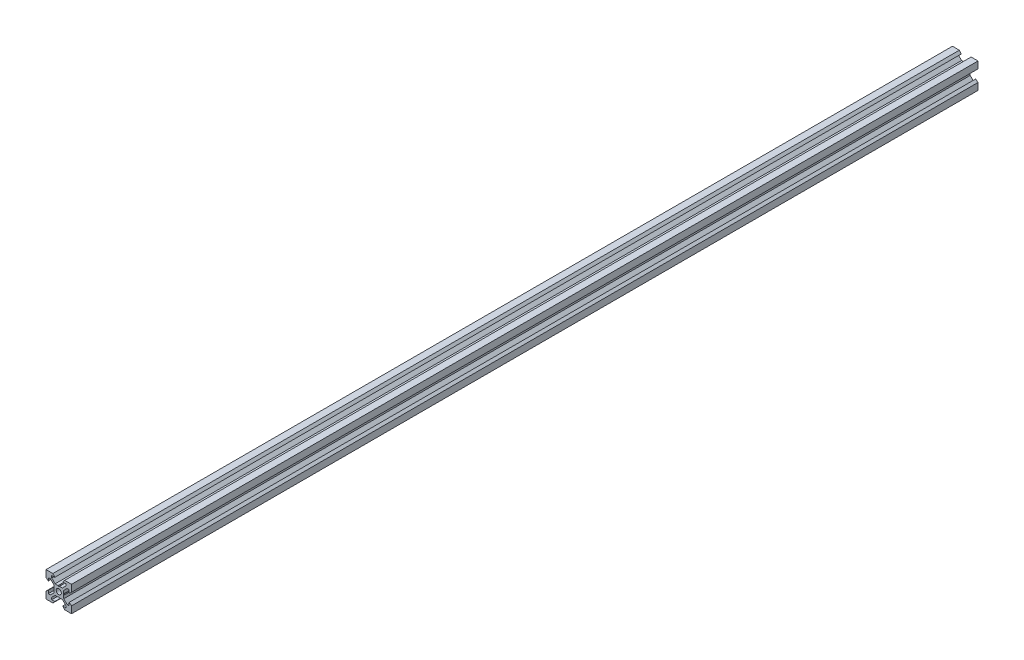
SolidWorks part; units mm, degrees
ref_plane "Front Plane" through (0, 0, 0) normal (0, 0, 1) x (1, 0, 0)
ref_plane "Top Plane" through (0, 0, 0) normal (0, 1, 0) x (1, 0, 0)
ref_plane "Right Plane" through (0, 0, 0) normal (1, 0, 0) x (0, 0, -1)
sketch "Sketch1" plane through (0, 0, 0) normal (0, 0, 1) x (1, 0, 0)
  line L0 (10, 10) -> (4.6104, 10) construction
  line L1 (10, 10) -> (10, 4.6104) construction
  line L2 (10, -10) -> (10, -4.6104) construction
  line L3 (10, -10) -> (4.6104, -10) construction
  line L4 (10, 10) -> (10, 4.6104)
  line L5 (6.5607, 5.5) -> (8.2, 5.5)
  line L6 (5.5, 8.2) -> (5.5, 6.5607)
  line L7 (10, 10) -> (4.6104, 10)
  line L8 (10, 10) -> (10, 4.6104)
  line L9 (6.5607, 5.5) -> (3.9, 2.8393)
  line L10 (5.5, 6.5607) -> (2.8393, 3.9)
  line L11 (10, 4.6104) -> (8.2, 3.1)
  line L12 (4.6104, 10) -> (3.1, 8.2)
  line L13 (8.2, 3.1) -> (8.2, 5.5)
  line L14 (3.1, 8.2) -> (5.5, 8.2)
  line L15 (-6.5607, 5.5) -> (-8.2, 5.5)
  line L16 (6.5607, -5.5) -> (8.2, -5.5)
  line L17 (3.1, -8.2) -> (5.5, -8.2)
  line L18 (8.2, -3.1) -> (8.2, -5.5)
  line L19 (4.6104, -10) -> (3.1, -8.2)
  line L20 (10, -4.6104) -> (8.2, -3.1)
  line L21 (0.5196, -3.9) -> (0, -3.6)
  line L22 (0.5196, 3.9) -> (0, 3.6)
  line L23 (3.6, 0) -> (3.9, -0.5196)
  line L24 (3.9, 0.5196) -> (3.6, 0)
  line L25 (3.9, 0.5196) -> (3.9, 2.8393)
  line L26 (2.8393, 3.9) -> (0.5196, 3.9)
  line L27 (3.9, -2.8393) -> (3.9, -0.5196)
  line L28 (2.8393, -3.9) -> (0.5196, -3.9)
  line L29 (5.5, -6.5607) -> (2.8393, -3.9)
  line L30 (6.5607, -5.5) -> (3.9, -2.8393)
  line L31 (10, -10) -> (10, -4.6104)
  line L32 (10, -10) -> (4.6104, -10)
  line L33 (5.5, -8.2) -> (5.5, -6.5607)
  line L34 (-6.5607, -5.5) -> (-8.2, -5.5)
  line L35 (10, -10) -> (10, -4.6104)
  line L36 (0, 0) -> (0, 8.2) construction
  line L37 (-10, -10) -> (-4.6104, -10) construction
  line L38 (-10, -10) -> (-10, -4.6104) construction
  line L39 (-10, 10) -> (-10, 4.6104) construction
  line L40 (-10, 10) -> (-4.6104, 10) construction
  line L41 (-10, -10) -> (-10, -4.6104)
  line L43 (-5.5, -8.2) -> (-5.5, -6.5607)
  line L44 (-10, -10) -> (-4.6104, -10)
  line L45 (-10, -10) -> (-10, -4.6104)
  line L46 (-6.5607, -5.5) -> (-3.9, -2.8393)
  line L47 (-5.5, -6.5607) -> (-2.8393, -3.9)
  line L48 (-2.8393, -3.9) -> (-0.5196, -3.9)
  line L49 (-3.9, -2.8393) -> (-3.9, -0.5196)
  line L50 (-2.8393, 3.9) -> (-0.5196, 3.9)
  line L51 (-3.9, 0.5196) -> (-3.9, 2.8393)
  line L52 (-3.9, 0.5196) -> (-3.6, 0)
  line L53 (-3.6, 0) -> (-3.9, -0.5196)
  line L54 (-0.5196, 3.9) -> (0, 3.6)
  line L55 (-0.5196, -3.9) -> (0, -3.6)
  line L56 (-10, -4.6104) -> (-8.2, -3.1)
  line L57 (-4.6104, -10) -> (-3.1, -8.2)
  line L58 (-8.2, -3.1) -> (-8.2, -5.5)
  line L59 (-3.1, -8.2) -> (-5.5, -8.2)
  line L60 (-10, -10) -> (10, -10) construction
  line L61 (-10, -10) -> (-10, 10) construction
  line L62 (-3.1, 8.2) -> (-5.5, 8.2)
  line L63 (-8.2, 3.1) -> (-8.2, 5.5)
  line L64 (-4.6104, 10) -> (-3.1, 8.2)
  line L65 (-10, 4.6104) -> (-8.2, 3.1)
  line L66 (-5.5, 6.5607) -> (-2.8393, 3.9)
  line L67 (-6.5607, 5.5) -> (-3.9, 2.8393)
  line L68 (-10, 10) -> (-10, 4.6104)
  line L69 (-10, 10) -> (-4.6104, 10)
  line L70 (-5.5, 8.2) -> (-5.5, 6.5607)
  line L71 (-10, 10) -> (10, 10) construction
  line L72 (-10, 10) -> (-10, 4.6104)
  line L73 (10, -10) -> (10, 10) construction
  line L74 (-10, -10) -> (10, 10) construction
  line L75 (-10, 10) -> (10, -10) construction
  circle A0 centre (0, 0) radius 2
  dimension "D7" = 4
  dimension "D1" = 20
  dimension "D2" = 5.3896
  dimension "D3" = 4.5
  dimension "D4" = 50
  dimension "D5" = 1.8
  dimension "D6" = 1.5104
  dimension "D8" = 5.5
  dimension "D9" = 120
  dimension "D10" = 0.3
  dimension "D11" = 2.3197
  dimension "D12" = 7.8
  dimension "D13" = 7.8
  dimension "D14" = 1.5
  dimension "D15" = 2.6607
extrude "Boss-Extrude1" add sketch "Sketch1" along normal mid plane 710 contours L70 L62 L64 L69 L68 L65 L63 L15 L67 L51 L52 L53 L49 L46 L34 L58 L56 L41 L44 L57 L59 L43 L47 L48 L55 L21 L28 L29 L33 L17 L19 L32 L31 L20 L18 L16 L30 L27 L23 L24 L25 L9 L5 L13 L11 L4 L7 L12 L14 L6 L10
